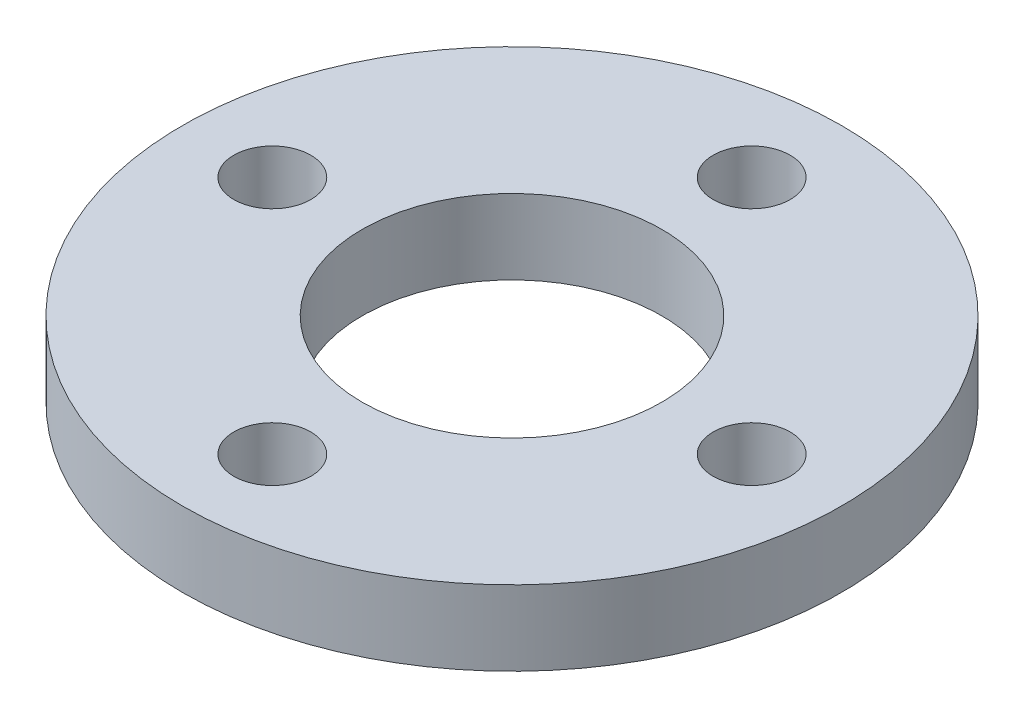
SolidWorks part; units mm, degrees
ref_plane "Front Plane" through (0, 0, 0) normal (0, 0, 1) x (1, 0, 0)
ref_plane "Top Plane" through (0, 0, 0) normal (0, 1, 0) x (1, 0, 0)
ref_plane "Right Plane" through (0, 0, 0) normal (1, 0, 0) x (0, 0, -1)
sketch "Sketch1" plane through (0, 0, 0) normal (0, 1, 0) x (1, 0, 0)
  circle A0 centre (0, 0) radius 13.97
  dimension "D1" = 27.94
extrude "Boss-Extrude1" add sketch "Sketch1" along normal blind 3.175
sketch "Sketch5" plane through (0, 3.175, 0) normal (0, 1, 0) x (1, 0, 0)
  circle A0 centre (0, 0) radius 6.35
  dimension "D1" = 12.7
extrude "Cut-Extrude2" cut sketch "Sketch5" against normal blind 3.175
hole_wizard "#4 Clearance Hole1" positions "Sketch7" profile "Sketch6" hole size "#4" standard "ANSI Inch"
sketch "Sketch7" plane through (0, 3.175, 0) normal (0, 1, 0) x (1, 0, 0)
  point P0 (10.16, 0)
  dimension "D1" = 10.16
sketch "Sketch6" plane through (10.16, 3.175, 0) normal (1, 0, 0) x (0, 0, 1)
  line L0 (0, 0) -> (0, 11.1406)
  line L1 (0, 11.1406) -> (1.6319, 10.16)
  line L2 (1.6319, 10.16) -> (1.6319, 0)
  line L5 (1.6319, 0) -> (0, 0)
  line L10 (0, 11.1406) -> (-1.632, 10.16) construction
  line L11 (0, -6.35) -> (0, 107.95) construction
  dimension "Hole Dia." = 3.2639
  dimension "Hole Depth" = 10.16
  dimension "Drill Angle" = 118
pattern_circular "CirPattern1" count 4 over 360 about axis through (0, 0, 0) along (0, 1, 0) of "#4 Clearance Hole1"
